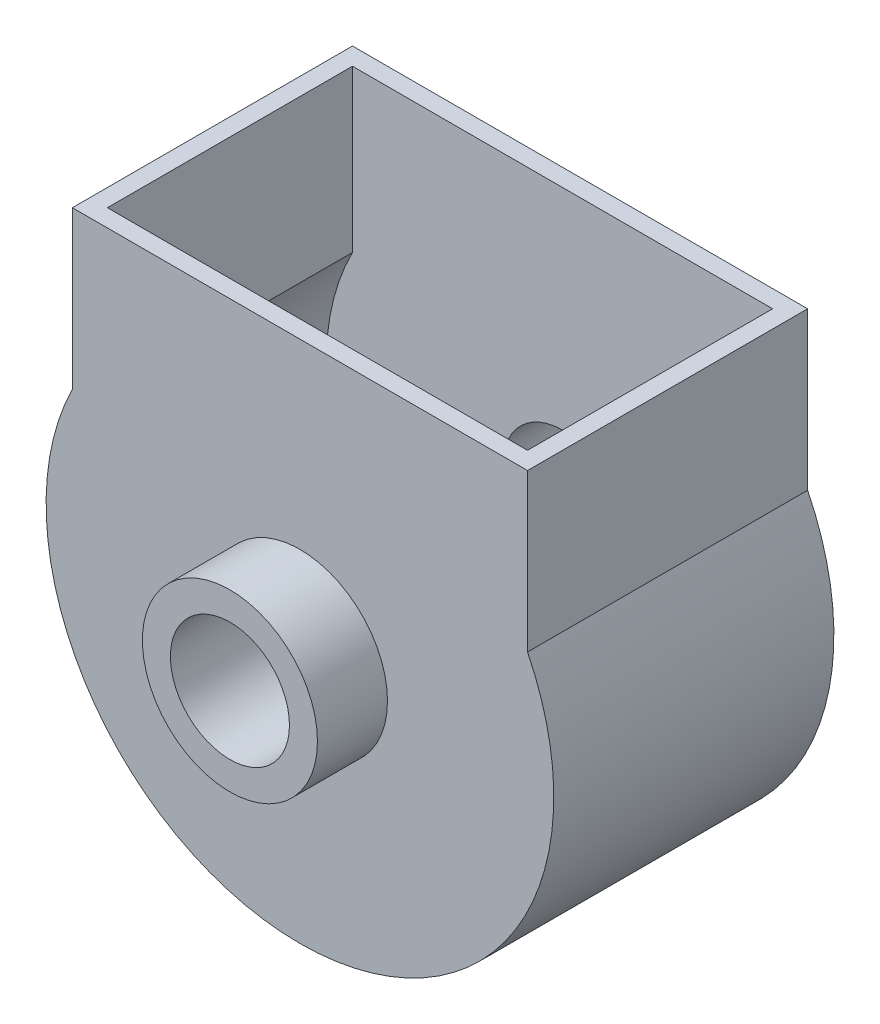
SolidWorks part; units mm, degrees
ref_plane "Front Plane" through (0, 0, 0) normal (0, 0, 1) x (1, 0, 0)
ref_plane "Top Plane" through (0, 0, 0) normal (0, 1, 0) x (1, 0, 0)
ref_plane "Right Plane" through (0, 0, 0) normal (1, 0, 0) x (0, 0, -1)
sketch "Sketch1" plane through (0, 0, 0) normal (0, 0, 1) x (1, 0, 0)
  circle A2 centre (0, 0) radius 250
  circle A3 centre (0, 0) radius 170
  dimension "D1" = 340
  dimension "D2" = 500
extrude "Boss-Extrude1" add sketch "Sketch1" along normal blind 200 and the other way blind 50 contours A2 A3
sketch "Sketch2" plane through (0, 0, 0) normal (0, 0, 1) x (1, 0, 0)
  line L2 (650, 770) -> (-650, 770)
  line L3 (-650, 770) -> (-650, 321.1308)
  line L4 (650, 770) -> (650, 321.1308)
  arc A0 (-650, 321.1308) -> (650, 321.1308) centre (0, 0) ccw
  circle A1 centre (0, 0) radius 250
  dimension "D1" = 1450
  dimension "D2" = 1300
  dimension "D3" = 448.8692
  dimension "D5" = 448.8692
extrude "Boss-Extrude3" add sketch "Sketch2" against normal blind 50 contours L3 A0 L4 L2 A1
ref_plane "Plane3" through (0, 0, -400) normal (0, 0, 1) x (1, 0, 0)
mirror "Mirror9" about plane through (0, 0, -400) normal (0, 0, 1) of bodies 106
sketch "Sketch4" plane through (0, 0, -400) normal (0, 0, 1) x (1, 0, 0)
  line L0 (0, 0) -> (0, 940.6394) construction
  line L2 (-600, 770) -> (-600, 309.2329)
  line L3 (600, 309.2329) -> (600, 770)
  line L5 (650, 321.1308) -> (650, 770)
  line L11 (-650, 770) -> (-650, 321.1308)
  line L12 (-650, 770) -> (-600, 770)
  line L13 (650, 770) -> (600, 770)
  arc A1 (-600, 309.2329) -> (600, 309.2329) centre (0, 0) ccw
  arc A5 (-650, 321.1308) -> (650, 321.1308) centre (0, 0) ccw
  dimension "D2" = 50
  dimension "D3" = 725
  dimension "D4" = 50
  dimension "D1" = 448.8692
extrude "Boss-Extrude4" add sketch "Sketch4" along normal up to next and the other way up to next contours A5 L5 L13 L3 A1 L2 L12 L11
